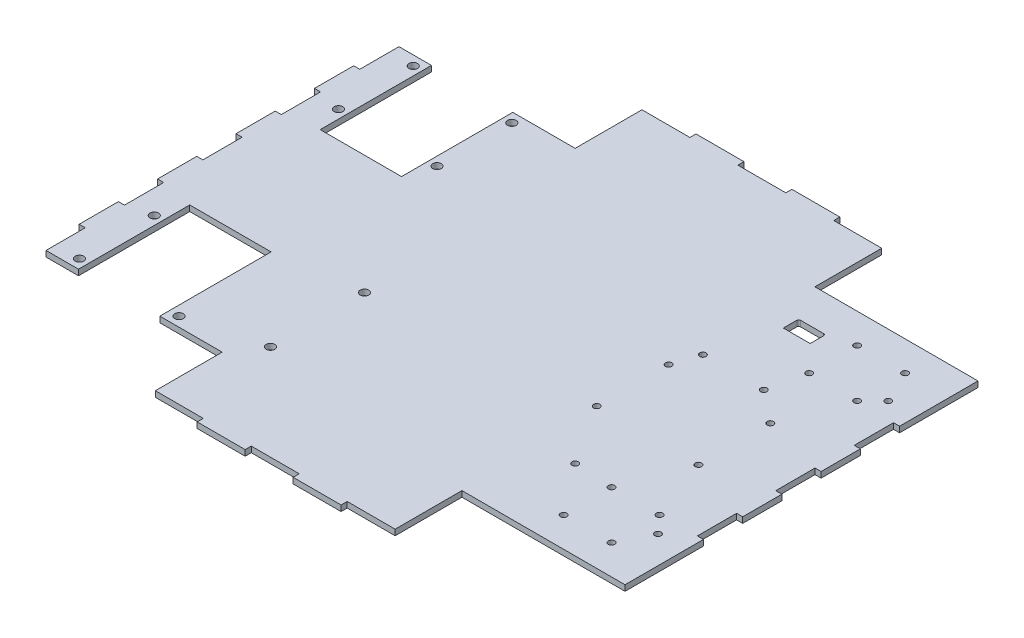
SolidWorks part; units mm, degrees
ref_plane "Front Plane" through (0, 0, 0) normal (0, 0, 1) x (1, 0, 0)
ref_plane "Top Plane" through (0, 0, 0) normal (0, 1, 0) x (1, 0, 0)
ref_plane "Right Plane" through (0, 0, 0) normal (1, 0, 0) x (0, 0, -1)
sketch "Sketch1" plane through (0, 0, 0) normal (0, 1, 0) x (1, 0, 0)
  line L0 (152.5, 92) -> (67.5, 92)
  line L1 (-152.5, -130) -> (152.5, -130)
  line L2 (-152.5, -130) -> (-152.5, 130)
  line L3 (-152.5, 130) -> (152.5, 130)
  line L4 (152.5, -130) -> (152.5, 130)
  line L5 (-152.5, -130) -> (152.5, 130) construction
  line L6 (-152.5, 130) -> (152.5, -130) construction
  line L7 (67.5, 92) -> (67.5, 130)
  line L8 (-152.5, 92) -> (-57.5, 92)
  line L9 (-57.5, 92) -> (-57.5, 130)
  line L10 (-152.5, -92) -> (-57.5, -92)
  line L11 (-57.5, -92) -> (-57.5, -130)
  line L12 (152.5, -92) -> (67.5, -92)
  line L13 (67.5, -92) -> (67.5, -130)
  line L14 (117.5, 64) -> (117.5, 92) construction
  line L31 (245.415, 41.2115) -> (245.415, -41.2115) construction
  line L37 (-111.1988, 130) -> (-111.1988, -130) construction
  line L39 (-149.325, 30.6667) -> (-149.325, 10.2222) construction
  line L40 (152.5, 10.2222) -> (149.325, 10.2222)
  line L41 (152.5, 10.2222) -> (152.5, -10.2222)
  line L42 (152.5, -10.2222) -> (149.325, -10.2222)
  line L43 (149.325, 10.2222) -> (149.325, -10.2222)
  line L44 (152.5, 51.1111) -> (149.325, 51.1111)
  line L45 (152.5, 51.1111) -> (152.5, 30.6667)
  line L46 (152.5, 30.6667) -> (149.325, 30.6667)
  line L47 (149.325, 51.1111) -> (149.325, 30.6667)
  line L48 (152.5, -30.6667) -> (149.325, -30.6667)
  line L49 (152.5, -30.6667) -> (152.5, -51.1111)
  line L50 (152.5, -51.1111) -> (149.325, -51.1111)
  line L51 (149.325, -30.6667) -> (149.325, -51.1111)
  line L52 (-149.325, 51.1111) -> (-152.5, 51.1111)
  line L53 (-149.325, 51.1111) -> (-149.325, 30.6667)
  line L54 (-149.325, 30.6667) -> (-152.5, 30.6667)
  line L55 (-152.5, 51.1111) -> (-152.5, 30.6667)
  line L56 (-149.325, 10.2222) -> (-152.5, 10.2222)
  line L57 (-149.325, 10.2222) -> (-149.325, -10.2222)
  line L58 (-149.325, -10.2222) -> (-152.5, -10.2222)
  line L59 (-152.5, 10.2222) -> (-152.5, -10.2222)
  line L60 (-149.325, -30.6667) -> (-152.5, -30.6667)
  line L61 (-149.325, -30.6667) -> (-149.325, -51.1111)
  line L62 (-149.325, -51.1111) -> (-152.5, -51.1111)
  line L63 (-152.5, -30.6667) -> (-152.5, -51.1111)
  line L64 (-149.325, -10.2222) -> (-149.325, -30.6667) construction
  line L65 (149.325, 30.6667) -> (149.325, 10.2222) construction
  line L66 (149.325, -10.2222) -> (149.325, -30.6667) construction
  line L67 (105, 51.5) -> (130, 51.5) construction
  line L68 (17.5, -130) -> (-7.5, -130)
  line L69 (17.5, -130) -> (17.5, -126.825)
  line L70 (17.5, -126.825) -> (-7.5, -126.825)
  line L71 (-7.5, -130) -> (-7.5, -126.825)
  line L72 (17.5, 130) -> (-7.5, 130)
  line L73 (17.5, 130) -> (17.5, 126.825)
  line L74 (17.5, 126.825) -> (-7.5, 126.825)
  line L75 (-7.5, 130) -> (-7.5, 126.825)
  line L76 (105, 51.5) -> (105, 76.5) construction
  line L77 (105, 76.5) -> (130, 76.5) construction
  line L95 (-136.8894, -48) -> (-136.8894, -87) construction
  line L104 (130, 51.5) -> (130, 76.5) construction
  line L105 (105, 51.5) -> (130, 76.5) construction
  line L116 (-132.3969, -34) -> (-90.0007, -34)
  line L117 (-132.3969, -34) -> (-132.3969, -92)
  line L118 (105, 76.5) -> (130, 51.5) construction
  line L119 (105, -76.5) -> (130, -76.5) construction
  line L120 (105, -76.5) -> (105, -51.5) construction
  line L121 (105, -51.5) -> (130, -51.5) construction
  line L122 (130, -76.5) -> (130, -51.5) construction
  line L123 (105, -76.5) -> (130, -51.5) construction
  line L124 (105, -51.5) -> (130, -76.5) construction
  line L126 (117.5, -64) -> (117.5, -92) construction
  line L128 (68.945, 32.131) -> (100.695, 32.131) construction
  line L129 (64.5, -18.75) -> (117.5, -18.75) construction
  line L130 (64.5, -18.75) -> (64.5, 18.75) construction
  line L131 (-149.325, 92) -> (-149.325, 71.5556)
  line L132 (-149.325, 71.5556) -> (-152.5, 71.5556)
  line L133 (-149.325, -92) -> (-149.325, -71.5556)
  line L134 (-149.325, -71.5556) -> (-152.5, -71.5556)
  line L135 (149.325, -92) -> (149.325, -71.5556)
  line L136 (149.325, -71.5556) -> (152.5, -71.5556)
  line L137 (149.325, 92) -> (149.325, 71.5556)
  line L138 (149.325, 71.5556) -> (152.5, 71.5556)
  line L139 (-57.5, -126.825) -> (-32.5, -126.825)
  line L140 (-32.5, -126.825) -> (-32.5, -130)
  line L141 (67.5, -126.825) -> (42.5, -126.825)
  line L142 (42.5, -126.825) -> (42.5, -130)
  line L143 (-57.5, -92) -> (67.5, -92) construction
  line L144 (-57.5, 126.825) -> (-32.5, 126.825)
  line L145 (-32.5, 126.825) -> (-32.5, 130)
  line L146 (67.5, 126.825) -> (42.5, 126.825)
  line L147 (42.5, 126.825) -> (42.5, 130)
  line L148 (-149.325, 71.5556) -> (-149.325, 51.1111) construction
  line L149 (-149.325, -71.5556) -> (-149.325, -51.1111) construction
  line L150 (-32.5, -126.825) -> (-7.5, -126.825) construction
  line L151 (17.5, -126.825) -> (42.5, -126.825) construction
  line L152 (-132.3969, -92) -> (-90.0007, -92)
  line L153 (229.54, -41.2115) -> (261.29, -41.2115) construction
  line L154 (64.5, 18.75) -> (117.5, 18.75) construction
  line L155 (117.5, -18.75) -> (117.5, 18.75) construction
  line L156 (64.5, -18.75) -> (117.5, 18.75) construction
  line L157 (64.5, 18.75) -> (117.5, -18.75) construction
  line L162 (-90.0007, -34) -> (-90.0007, -92)
  line L164 (64.5, 64.643) -> (143.24, 64.643) construction
  line L165 (64.5, 64.643) -> (64.5, -64.643) construction
  line L166 (64.5, -64.643) -> (143.24, -64.643) construction
  line L167 (143.24, 64.643) -> (143.24, -64.643) construction
  line L168 (64.5, 64.643) -> (143.24, -64.643) construction
  line L169 (64.5, -64.643) -> (143.24, 64.643) construction
  line L170 (84.82, -50.289) -> (84.82, 32.131) construction
  line L171 (143.24, 59.563) -> (138.16, 59.563) construction
  line L172 (138.16, 59.563) -> (138.16, 64.643) construction
  line L173 (143.24, -60.452) -> (138.16, -60.452) construction
  line L174 (138.16, -60.452) -> (138.16, -64.643) construction
  line L176 (77.88, 65.143) -> (91.88, 65.143)
  line L177 (77.88, 65.143) -> (77.88, 72.143)
  line L178 (78.88, 73.143) -> (90.88, 73.143)
  line L179 (91.88, 65.143) -> (91.88, 72.143)
  line L180 (77.88, 65.143) -> (91.88, 73.143) construction
  line L181 (77.88, 73.143) -> (91.88, 65.143) construction
  line L184 (-132.3969, -34) -> (-90.0007, -92) construction
  line L185 (-132.3969, -92) -> (-90.0007, -34) construction
  line L190 (-136.8894, -87) -> (-85.0006, -87) construction
  line L191 (-47.3083, -77) -> (-47.3083, -28) construction
  line L193 (-132.3969, 34) -> (-90.0007, 34)
  line L194 (-132.3969, 34) -> (-132.3969, 92)
  line L195 (-132.3969, 92) -> (-90.0007, 92)
  line L196 (-90.0007, 34) -> (-90.0007, 92)
  line L197 (-132.3969, 34) -> (-90.0007, 92) construction
  line L198 (-132.3969, 92) -> (-90.0007, 34) construction
  line L200 (-136.8895, 48) -> (-85.5082, 48) construction
  line L201 (-136.8895, 48) -> (-136.8895, 87) construction
  line L202 (-136.8895, 87) -> (-85.5082, 87) construction
  line L203 (-85.5082, 48) -> (-85.5082, 87) construction
  line L204 (-136.8895, 48) -> (-85.5082, 87) construction
  line L205 (-136.8895, 87) -> (-85.5082, 48) construction
  circle A26 centre (105, 76.5) radius 1.65
  circle A27 centre (130, 76.5) radius 1.65
  circle A28 centre (130, 51.5) radius 1.65
  circle A29 centre (105, 51.5) radius 1.65
  circle A30 centre (105, -51.5) radius 1.65
  circle A31 centre (130, -51.5) radius 1.65
  circle A32 centre (130, -76.5) radius 1.65
  circle A33 centre (105, -76.5) radius 1.65
  circle A37 centre (245.415, 41.2115) radius 1.65
  circle A38 centre (229.54, -41.2115) radius 1.65
  circle A39 centre (261.29, -41.2115) radius 1.65
  circle A40 centre (117.5, 18.75) radius 1.65
  circle A41 centre (117.5, -18.75) radius 1.65
  circle A42 centre (64.5, -18.75) radius 1.65
  circle A43 centre (64.5, 18.75) radius 1.65
  circle A44 centre (68.945, 32.131) radius 1.65
  circle A45 centre (100.695, 32.131) radius 1.65
  circle A46 centre (138.16, 59.563) radius 1.65
  circle A47 centre (84.82, -50.289) radius 1.65
  circle A48 centre (138.16, -60.452) radius 1.65
  arc A51 (90.88, 73.143) -> (91.88, 72.143) centre (90.88, 72.143) cw
  arc A52 (77.88, 72.143) -> (78.88, 73.143) centre (78.88, 72.143) cw
  circle A63 centre (-136.8894, -48) radius 2.25
  circle A64 centre (-136.8894, -87) radius 2.25
  circle A65 centre (-85.0006, -87) radius 2.25
  circle A66 centre (-47.3083, -77) radius 2.25
  circle A67 centre (-47.3083, -28) radius 2.25
  circle A68 centre (-136.8895, 87) radius 2.25
  circle A69 centre (-136.8895, 48) radius 2.25
  circle A70 centre (-85.5082, 87) radius 2.25
  circle A71 centre (-85.5082, 48) radius 2.25
  point P0 (0, 0)
  point P26 (117.5, -64)
  point P31 (-111.1988, -63)
  point P33 (-111.1988, 63)
  point P34 (-111.1988, 67.5)
  point P38 (117.5, 64)
  point P43 (149.325, 0)
  point P68 (5, -126.825)
  point P110 (91, 0)
  point P127 (245.415, 0)
  point P145 (5, -92)
  point P153 (103.87, 0)
  point P156 (245.415, -41.2115)
  point P188 (84.88, 65.143)
  point P197 (84.88, 69.143)
  dimension "D12" = 85
  dimension "D14" = 42.3962
  dimension "D16" = 5
  dimension "D21" = 3.3
  dimension "D24" = 3.3
  dimension "D37" = 39
  dimension "D26" = 1
  dimension "D45" = 49
  dimension "D15" = 82.423
  dimension "D17" = 25.6906
  dimension "D7" = 51.3813
  dimension "D5" = 4.5
  dimension "D1" = 305
  dimension "D2" = 260
  dimension "D3" = 38
  dimension "D4" = 95
  dimension "D6" = 41.3012
  dimension "D8" = 31.75
  dimension "D9" = 3.175
  dimension "D10" = 39
  dimension "D11" = 3.175
  dimension "D13" = 25
  dimension "D19" = 28
  dimension "D20" = 35
  dimension "D22" = 37.5
  dimension "D23" = 82.423
  dimension "D25" = 53
  dimension "D27" = 42.3962
  dimension "D28" = 58
  dimension "D29" = 129.286
  dimension "D30" = 78.74
  dimension "D31" = 31.75
  dimension "D32" = 82.42
  dimension "D33" = 4.445
  dimension "D34" = 32.512
  dimension "D35" = 5.08
  dimension "D36" = 4.191
  dimension "D38" = 5
  dimension "D39" = 8
  dimension "D40" = 14
  dimension "D41" = 20.38
  dimension "D42" = 1
  dimension "D43" = 4.4925
  dimension "D44" = 51.8888
  dimension "D47" = 37.6923
  dimension "D48" = 10
extrude "Boss-Extrude1" add sketch "Sketch1" along normal blind 3
